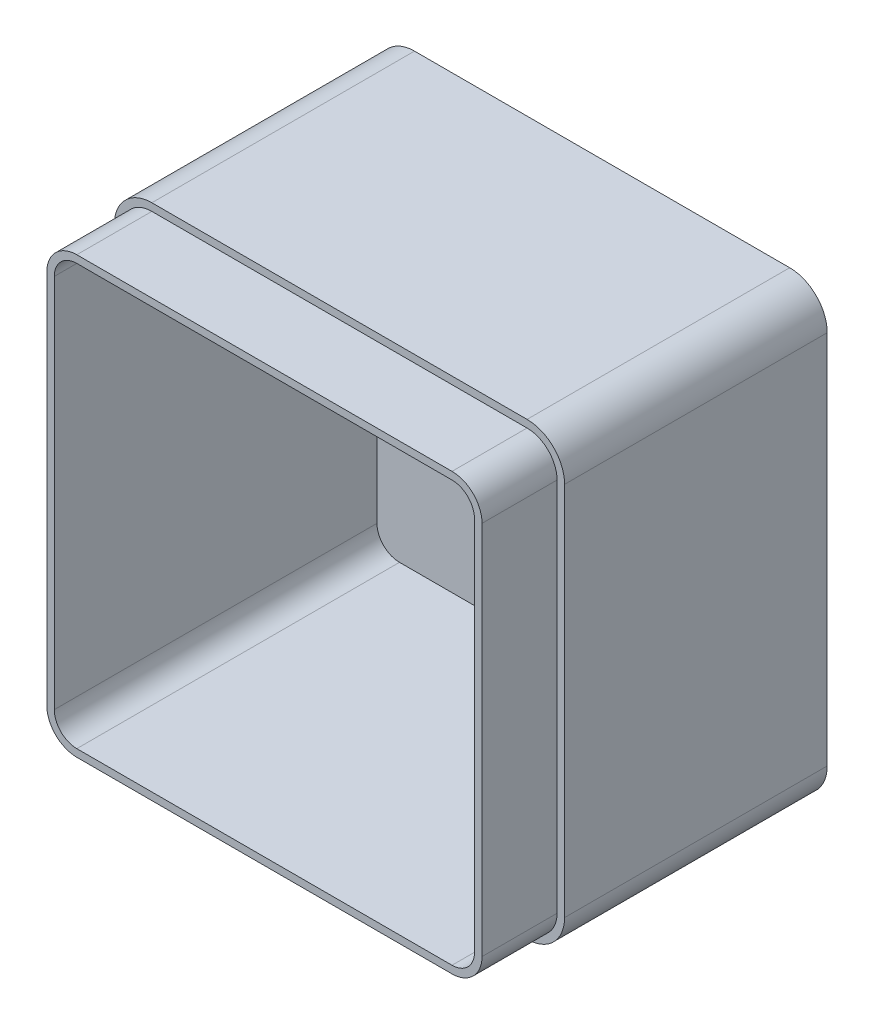
SolidWorks part; units mm, degrees
ref_plane "Front" through (0, 0, 0) normal (0, 0, 1) x (1, 0, 0)
ref_plane "Top" through (0, 0, 0) normal (0, 1, 0) x (1, 0, 0)
ref_plane "Right" through (0, 0, 0) normal (1, 0, 0) x (0, 0, -1)
sketch "Sketch1" plane through (0, 0, 0) normal (0, 0, 1) x (1, 0, 0)
  line L1 (0, 0) -> (120, 0)
  line L2 (0, 0) -> (0, 120)
  line L3 (0, 120) -> (120, 120)
  line L4 (120, 0) -> (120, 120)
  dimension "D1" = 120
  dimension "D2" = 120
extrude "Boss-Extrude1" add sketch "Sketch1" along normal blind 90
fillet "Fillet1" radius 10 4 edges at (120, 0, 45) (120, 120, 45) (0, 0, 45) (0, 120, 45)
shell "Shell1" thickness 4
sketch "Sketch7" plane through (0, 0, 90) normal (0, 0, 1) x (1, 0, 0)
  line L4 (10, 0) -> (110, 0)
  line L5 (120, 10) -> (120, 110)
  line L6 (110, 120) -> (10, 120)
  line L7 (0, 110) -> (0, 10)
  line L8 (10, 0) -> (110, 0)
  line L9 (120, 10) -> (120, 110)
  line L10 (110, 120) -> (10, 120)
  line L11 (0, 110) -> (0, 10)
  line L16 (10, 2) -> (110, 2)
  line L17 (118, 10) -> (118, 110)
  line L18 (110, 118) -> (10, 118)
  line L19 (2, 110) -> (2, 10)
  line L20 (10, 2) -> (110, 2)
  line L21 (118, 10) -> (118, 110)
  line L22 (110, 118) -> (10, 118)
  line L23 (2, 110) -> (2, 10)
  arc A4 (110, 0) -> (120, 10) centre (110, 10) ccw
  arc A5 (120, 110) -> (110, 120) centre (110, 110) ccw
  arc A6 (10, 120) -> (0, 110) centre (10, 110) ccw
  arc A7 (0, 10) -> (10, 0) centre (10, 10) ccw
  arc A8 (110, 0) -> (120, 10) centre (110, 10) ccw
  arc A9 (120, 110) -> (110, 120) centre (110, 110) ccw
  arc A10 (10, 120) -> (0, 110) centre (10, 110) ccw
  arc A11 (0, 10) -> (10, 0) centre (10, 10) ccw
  arc A16 (110, 2) -> (118, 10) centre (110, 10) ccw
  arc A17 (118, 110) -> (110, 118) centre (110, 110) ccw
  arc A18 (10, 118) -> (2, 110) centre (10, 110) ccw
  arc A19 (2, 10) -> (10, 2) centre (10, 10) ccw
  arc A20 (110, 2) -> (118, 10) centre (110, 10) ccw
  arc A21 (118, 110) -> (110, 118) centre (110, 110) ccw
  arc A22 (10, 118) -> (2, 110) centre (10, 110) ccw
  arc A23 (2, 10) -> (10, 2) centre (10, 10) ccw
  dimension "D1" = 0
  dimension "D2" = 2
extrude "Cut-Extrude3" cut sketch "Sketch7" against normal blind 20
sketch "Sketch3" plane through (0, 0, 90) normal (0, 0, 1) x (1, 0, 0)
  line L4 (10, 0) -> (110, 0)
  line L5 (120, 10) -> (120, 110)
  line L6 (110, 120) -> (10, 120)
  line L7 (0, 110) -> (0, 10)
  line L8 (10, 0) -> (110, 0)
  line L9 (120, 10) -> (120, 110)
  line L10 (110, 120) -> (10, 120)
  line L11 (0, 110) -> (0, 10)
  line L16 (10, 2) -> (110, 2)
  line L17 (118, 10) -> (118, 110)
  line L18 (110, 118) -> (10, 118)
  line L19 (2, 110) -> (2, 10)
  line L20 (10, 2) -> (110, 2)
  line L21 (118, 10) -> (118, 110)
  line L22 (110, 118) -> (10, 118)
  line L23 (2, 110) -> (2, 10)
  arc A4 (110, 0) -> (120, 10) centre (110, 10) ccw
  arc A5 (120, 110) -> (110, 120) centre (110, 110) ccw
  arc A6 (10, 120) -> (0, 110) centre (10, 110) ccw
  arc A7 (0, 10) -> (10, 0) centre (10, 10) ccw
  arc A8 (110, 0) -> (120, 10) centre (110, 10) ccw
  arc A9 (120, 110) -> (110, 120) centre (110, 110) ccw
  arc A10 (10, 120) -> (0, 110) centre (10, 110) ccw
  arc A11 (0, 10) -> (10, 0) centre (10, 10) ccw
  arc A16 (110, 2) -> (118, 10) centre (110, 10) ccw
  arc A17 (118, 110) -> (110, 118) centre (110, 110) ccw
  arc A18 (10, 118) -> (2, 110) centre (10, 110) ccw
  arc A19 (2, 10) -> (10, 2) centre (10, 10) ccw
  arc A20 (110, 2) -> (118, 10) centre (110, 10) ccw
  arc A21 (118, 110) -> (110, 118) centre (110, 110) ccw
  arc A22 (10, 118) -> (2, 110) centre (10, 110) ccw
  arc A23 (2, 10) -> (10, 2) centre (10, 10) ccw
  dimension "D1" = 0
  dimension "D2" = 2
